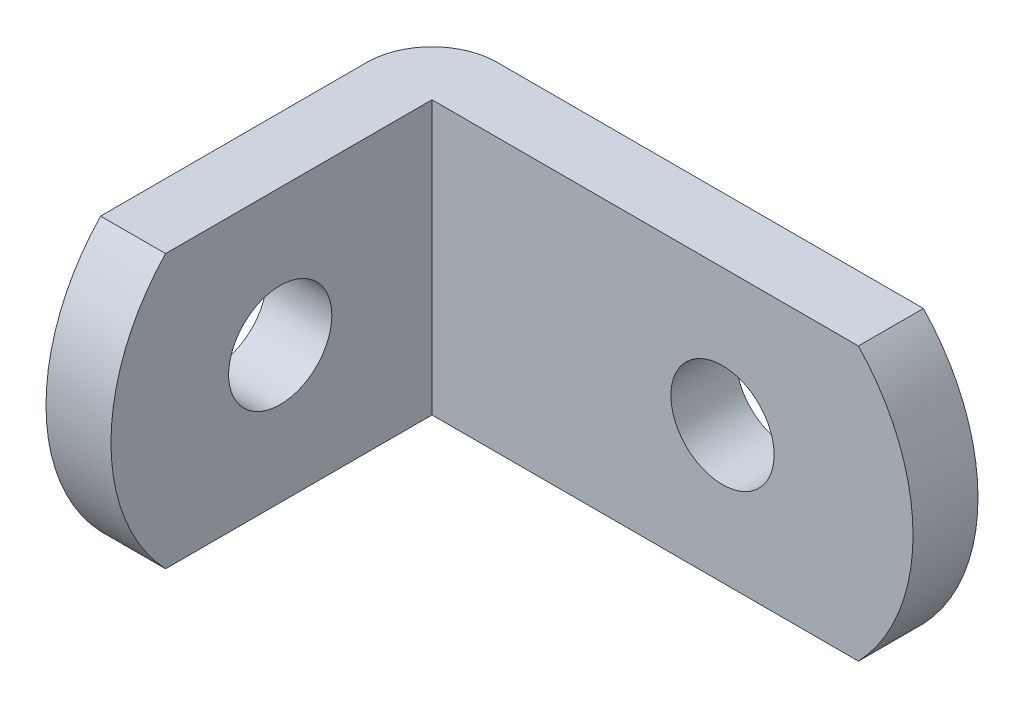
SolidWorks part; units mm, degrees
ref_plane "Front Plane" through (0, 0, 0) normal (0, 0, 1) x (1, 0, 0)
ref_plane "Top Plane" through (0, 0, 0) normal (0, 1, 0) x (1, 0, 0)
ref_plane "Right Plane" through (0, 0, 0) normal (1, 0, 0) x (0, 0, -1)
sketch "Sketch1" plane through (0, 0, 0) normal (0, 1, 0) x (1, 0, 0)
  line L0 (0, -3.0226) -> (0, -17.9578)
  line L1 (3.0226, 0) -> (25.4, 0)
  line L2 (0, -17.9578) -> (3.0226, -17.9578) construction
  arc A0 (0, -3.0226) -> (3.0226, 0) centre (3.0226, -3.0226) cw
  point P7 (0, 0)
  dimension "D1" = 3.0226
  dimension "Length (A)" = 17.9578
  dimension "Length (B)" = 25.4
  dimension "Thickness" = 3.0226
sketch "Sketch2" plane through (0, 0, 0) normal (0, 0, 1) x (1, 0, 0)
  line L0 (25.4, -6.35) -> (25.4, 6.35) construction
  line L1 (3.0226, 0) -> (25.4, 0) construction
  circle A0 centre (16.5354, 0) radius 2.4
  arc A1 (22.86, 6.35) -> (22.86, -6.35) centre (16.1925, 0) cw
  point P4 (25.4, 0)
  dimension "Hole Size" = 4.8
  dimension "D2" = 9.2075
  dimension "Length (C)" = 12.7
  dimension "A2 Hole Offset" = 8.8646
  dimension "D1" = 2.54
sketch "Sketch3" plane through (0, 0, 0) normal (1, 0, 0) x (0, 0, -1)
  line L0 (-3.0226, 0) -> (-17.9578, 0) construction
  line L2 (-17.9578, 6.35) -> (-17.9578, -6.35) construction
  line L3 (0, -6.35) -> (0, 6.35) construction
  circle A0 centre (-10.0838, 0) radius 2.4
  arc A1 (-15.4178, 6.35) -> (-15.4178, -6.35) centre (-8.7503, 0) ccw
  point P14 (-17.9578, 0)
  dimension "D1" = 4.8
  dimension "A1 Hole Offset" = 7.874
  dimension "D2" = 2.54
sketch "Sketch4" plane through (0, 0, 0) normal (0, 1, 0) x (1, 0, 0)
  line L0 (0, -3.0226) -> (0, -17.9578) construction
  line L1 (3.0226, 0) -> (25.4, 0) construction
  line L2 (0, -3.0226) -> (0, -17.9578)
  line L3 (3.0226, 0) -> (25.4, 0)
  arc A0 (3.0226, 0) -> (0, -3.0226) centre (3.0226, -3.0226) ccw construction
  arc A1 (3.0226, 0) -> (0, -3.0226) centre (3.0226, -3.0226) ccw
extrude "Extrude-Thin1" add sketch "Sketch4" along normal mid plane 12.7 thin
sketch "Sketch5" plane through (3.0226, 0, 0) normal (1, 0, 0) x (0, 0, -1)
  arc A0 (-15.4178, 6.35) -> (-15.4178, -6.35) centre (-8.7503, 0) ccw construction
  arc A1 (-15.4178, 6.35) -> (-15.4178, -6.35) centre (-8.7503, 0) ccw
extrude "Cut-Extrude1" cut sketch "Sketch5" against normal through all and the other way through all flip side to cut
sketch "Sketch7" plane through (3.0226, 0, 0) normal (1, 0, 0) x (0, 0, -1)
  circle A0 centre (-10.0838, 0) radius 2.4 construction
  circle A1 centre (-10.0838, 0) radius 2.4
extrude "Cut-Extrude3" cut sketch "Sketch7" against normal through all
sketch "Sketch6" plane through (0, 0, 3.0226) normal (0, 0, 1) x (1, 0, 0)
  arc A0 (22.86, -6.35) -> (22.86, 6.35) centre (16.1925, 0) ccw construction
  arc A1 (22.86, -6.35) -> (22.86, 6.35) centre (16.1925, 0) ccw
extrude "Cut-Extrude2" cut sketch "Sketch6" against normal through all and the other way through all flip side to cut
sketch "Sketch8" plane through (0, 0, 3.0226) normal (0, 0, 1) x (1, 0, 0)
  circle A0 centre (16.5354, 0) radius 2.4 construction
  circle A1 centre (16.5354, 0) radius 2.4
extrude "Cut-Extrude4" cut sketch "Sketch8" against normal through all
equation "\"D1@Sketch1\" = \"Thickness@Sketch1\"*1"
equation "\"D1@Sketch3\"=\"Hole Size@Sketch2\""
equation "\"D1@Sketch2\"=\"Length (C)@Sketch2\"*.2"
equation "\"D2@Sketch3\"=\"D1@Sketch2\""
equation "\"D5@Extrude-Thin1\"=\"Thickness@sketch1\""
equation "\"D1@Extrude-Thin1\"=\"Length (C)@Sketch2\""
